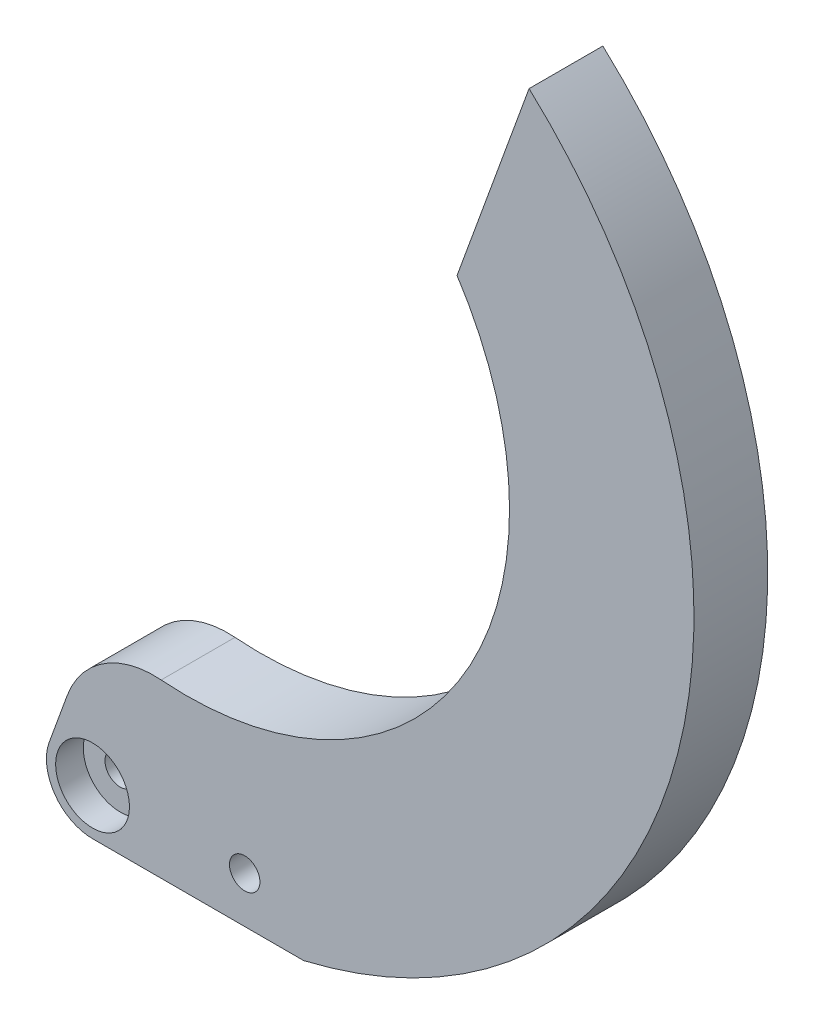
SolidWorks part; units mm, degrees
ref_plane "前基準面" through (0, 0, 0) normal (0, 0, 1) x (1, 0, 0)
ref_plane "上基準面" through (0, 0, 0) normal (0, 1, 0) x (1, 0, 0)
ref_plane "右基準面" through (0, 0, 0) normal (1, 0, 0) x (0, 0, -1)
sketch "草圖1" plane through (0, 0, 0) normal (0, 0, 1) x (1, 0, 0)
  line L0 (0, -5) -> (22.8963, -5)
  line L1 (47.3346, 89.1031) -> (39.5253, 67.6471)
  line L2 (-4.6985, 1.7101) -> (0.1387, 15)
  line L3 (10.2152, 48.5181) -> (2.4058, 27.0621) construction
  line L4 (0, 0) -> (45.7917, 0) construction
  line L5 (45.7917, 0) -> (0, 0) construction
  line L6 (0, 0) -> (16.5, 0) construction
  line L7 (10.2152, 48.5181) -> (-2.3417, 53.0884) construction
  circle A0 centre (0, 0) radius 1.65
  arc A1 (-4.6985, 1.7101) -> (0, -5) centre (0, 0) ccw
  arc A2 (0.1387, 15) -> (39.5253, 67.6471) centre (10.2152, 48.5181) ccw
  arc A3 (22.8963, -5) -> (47.3346, 89.1031) centre (10.2152, 48.5181) ccw
  circle A4 centre (16.5, 0) radius 1.65
  dimension "D2" = 35
  dimension "D6" = 3.3
  dimension "D7" = 5
  dimension "D8" = 20
  dimension "D4" = 5
  dimension "D5" = 1.9951
  dimension "D9" = 55
  dimension "D1" = 70
  dimension "D3" = 16.5
  dimension "D10" = 42
extrude "填料-伸長1" add sketch "草圖1" along normal blind 8
fillet "圓角1" radius 10 1 edges at (0.1387, 15, 4)
sketch "草圖2" plane through (0, 0, 8) normal (0, 0, -1) x (-1, 0, 0)
  circle A0 centre (0, 0) radius 4
  dimension "D1" = 8
extrude "除料-伸長1" cut sketch "草圖2" along normal blind 3
